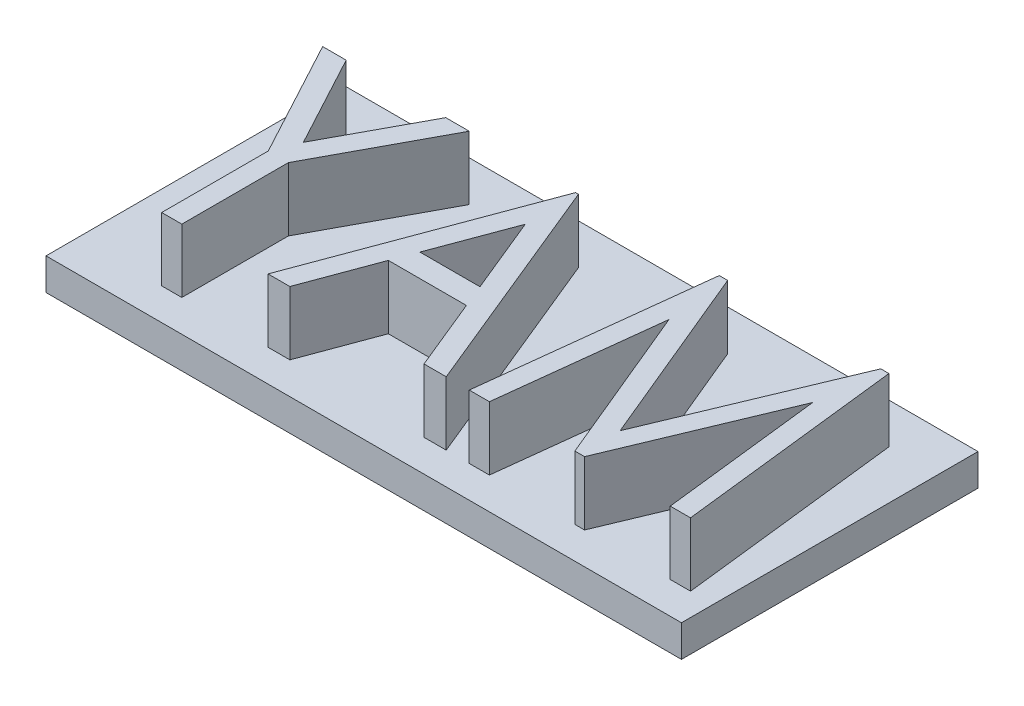
SolidWorks part; units mm, degrees
ref_plane "Front Plane" through (0, 0, 0) normal (0, 0, 1) x (1, 0, 0)
ref_plane "Top Plane" through (0, 0, 0) normal (0, 1, 0) x (1, 0, 0)
ref_plane "Right Plane" through (0, 0, 0) normal (1, 0, 0) x (0, 0, -1)
sketch "Sketch1" plane through (0, 0, 0) normal (0, 1, 0) x (1, 0, 0)
  line L1 (-7.5, 3.5) -> (7.5, 3.5)
  line L2 (-7.5, 3.5) -> (-7.5, -3.5)
  line L3 (-7.5, -3.5) -> (7.5, -3.5)
  line L4 (7.5, 3.5) -> (7.5, -3.5)
  line L5 (-7.5, 3.5) -> (7.5, -3.5) construction
  line L6 (-7.5, -3.5) -> (7.5, 3.5) construction
  point P0 (0, 0)
extrude "Boss-Extrude1" add sketch "Sketch1" along normal blind 0.75
sketch "Sketch2" plane through (0, 0.75, 0) normal (0, 1, 0) x (1, 0, 0)
  text T0 "MAY" font "Century Gothic" height in points 20
extrude "Boss-Extrude2" add sketch "Sketch2" along normal blind 1.5
